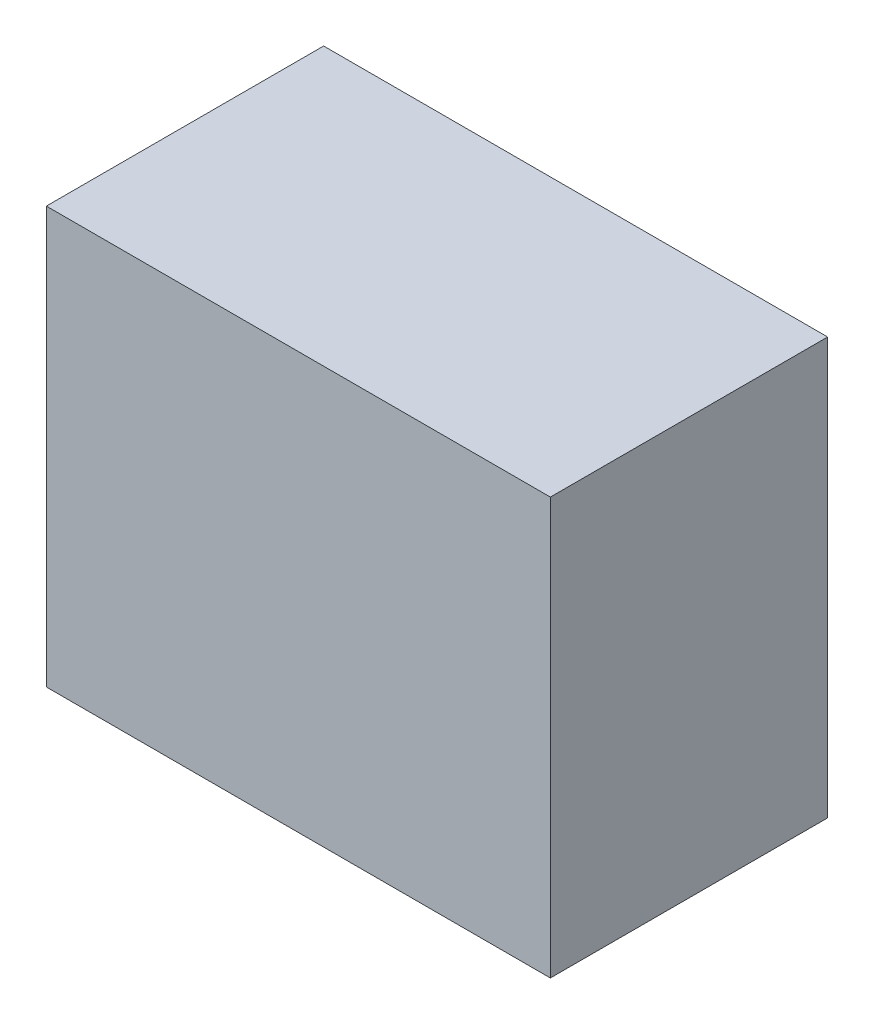
SolidWorks part; units mm, degrees
ref_plane "Front Plane" through (0, 0, 0) normal (0, 0, 1) x (1, 0, 0)
ref_plane "Top Plane" through (0, 0, 0) normal (0, 1, 0) x (1, 0, 0)
ref_plane "Right Plane" through (0, 0, 0) normal (1, 0, 0) x (0, 0, -1)
sketch "Sketch2" plane through (0, 0, 0) normal (0, 0, 1) x (1, 0, 0)
  line L1 (-164.592, 136.017) -> (164.592, 136.017)
  line L2 (-164.592, 136.017) -> (-164.592, -136.017)
  line L3 (-164.592, -136.017) -> (164.592, -136.017)
  line L4 (164.592, 136.017) -> (164.592, -136.017)
  line L5 (-164.592, 136.017) -> (164.592, -136.017) construction
  line L6 (-164.592, -136.017) -> (164.592, 136.017) construction
  point P0 (0, 0)
  dimension "D1" = 329.184
  dimension "D2" = 272.034
extrude "Boss-Extrude1" add sketch "Sketch2" along normal blind 181.102
